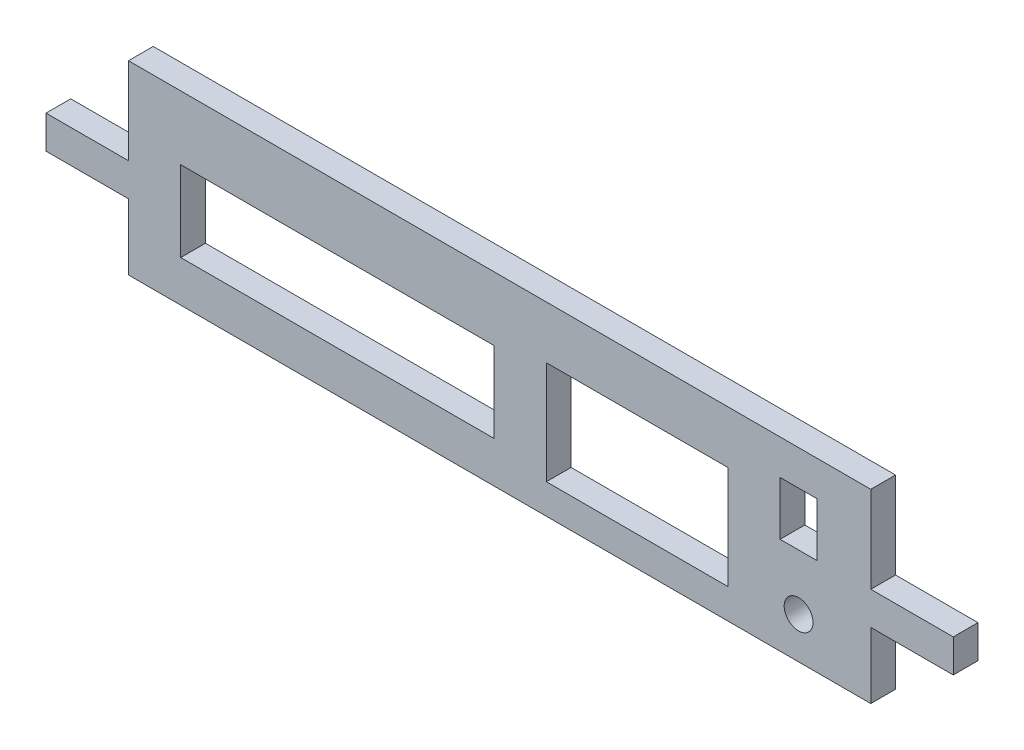
SolidWorks part; units mm, degrees
material "Balsa"
ref_plane "Plano frontal" through (0, 0, 0) normal (0, 0, 1) x (1, 0, 0)
ref_plane "Plano superior" through (0, 0, 0) normal (0, 1, 0) x (1, 0, 0)
ref_plane "Plano direito" through (0, 0, 0) normal (1, 0, 0) x (0, 0, -1)
sketch "Esboço1" plane through (0, 0, 0) normal (0, 0, 1) x (1, 0, 0)
  line L0 (-90, -6.5) -> (-90, -22.5)
  line L1 (-90, -6.5) -> (-110, -6.5)
  line L2 (-90, 22.5) -> (-90, 1.5)
  line L3 (-90, -22.5) -> (90, -22.5)
  line L4 (90, 22.5) -> (90, 1.5)
  line L5 (90, 1.5) -> (110, 1.5)
  line L6 (-90, -22.5) -> (90, 22.5) construction
  line L7 (-90, 1.5) -> (-110, 1.5)
  line L8 (-110, -6.5) -> (-110, 1.5)
  line L9 (90, -6.5) -> (110, -6.5)
  line L10 (110, -6.5) -> (110, 1.5)
  line L11 (90, -6.5) -> (90, -22.5)
  line L12 (0, 0) -> (0, 44.2972) construction
  line L13 (-90, -8.503) -> (-77.3333, -8.503) construction
  line L14 (-1.3333, -8.503) -> (11.3333, -8.503) construction
  line L15 (55.3333, 4.4718) -> (68, 4.4718) construction
  line L20 (-90, 22.5) -> (90, 22.5)
  line L47 (-90, 22.5) -> (90, -22.5) construction
  line L48 (-77.3333, -12.5) -> (-1.3333, -12.5)
  line L49 (-77.3333, -12.5) -> (-77.3333, 7)
  line L50 (-77.3333, 7) -> (-1.3333, 7)
  line L51 (-1.3333, -12.5) -> (-1.3333, 7)
  line L52 (-77.3333, -12.5) -> (-1.3333, 7) construction
  line L53 (-77.3333, 7) -> (-1.3333, -12.5) construction
  line L54 (11.3333, 9.75) -> (55.3333, 9.75)
  line L55 (11.3333, 9.75) -> (11.3333, -15.25)
  line L56 (11.3333, -15.25) -> (55.3333, -15.25)
  line L57 (55.3333, 9.75) -> (55.3333, -15.25)
  line L58 (11.3333, 9.75) -> (55.3333, -15.25) construction
  line L59 (11.3333, -15.25) -> (55.3333, 9.75) construction
  line L60 (68, 14) -> (77, 14)
  line L61 (68, 14) -> (68, 1)
  line L62 (68, 1) -> (77, 1)
  line L63 (77, 14) -> (77, 1)
  line L64 (68, 14) -> (77, 1) construction
  line L65 (68, 1) -> (77, 14) construction
  circle A0 centre (72.5, -12.5) radius 3.5
  point P0 (0, 0)
  point P16 (0, 0)
  point P25 (72.5, 7.5)
  point P37 (33.3333, -2.75)
  point P54 (-39.3333, -2.75)
  dimension "D22" = 7
  dimension "D3" = 180
  dimension "D4" = 45
  dimension "D5" = 20
  dimension "D6" = 8
  dimension "D7" = 16
  dimension "D13" = 19.5
  dimension "D14" = 76
  dimension "D16" = 10
  dimension "D17" = 44
  dimension "D18" = 25
  dimension "D20" = 13
  dimension "D21" = 9
  dimension "D23" = 13
  dimension "D24" = 10
  dimension "D25" = 20
extrude "Ressalto-extrusão1" add sketch "Esboço1" along normal blind 6
